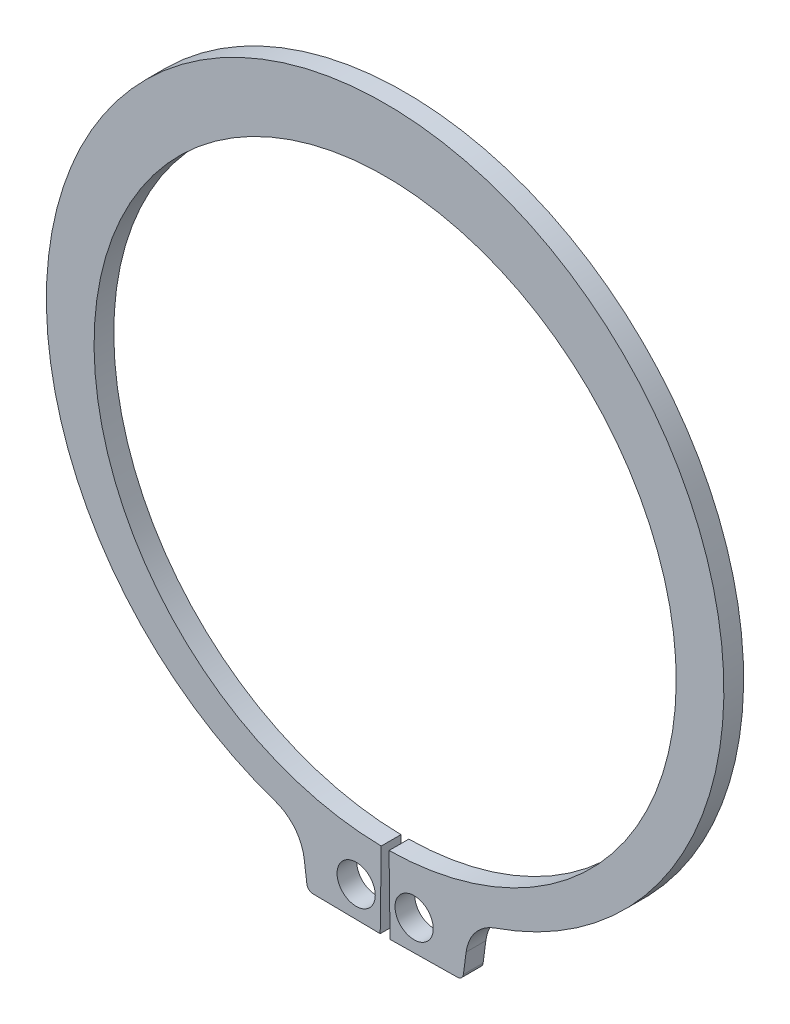
SolidWorks part; units mm, degrees
ref_plane "Plane1" through (0, 0, 0) normal (0, 0, 1) x (1, 0, 0)
ref_plane "Plane2" through (0, 0, 0) normal (0, 1, 0) x (1, 0, 0)
ref_plane "Plane3" through (0, 0, 0) normal (1, 0, 0) x (0, 0, -1)
sketch "Clipboard" plane through (0, 0, 0) normal (0, 0, 1) x (1, 0, 0)
  line L0 (0, 0) -> (5.1, 0)
  line L1 (0, 0) -> (0, 2.7)
  line L2 (0, 0) -> (0, -6.2)
  circle A0 centre (0, 0) radius 1.55
  circle A1 centre (0, 0) radius 25
  dimension "HoleDia" = 3.1
  dimension "ShaftDia" = 50
  dimension "LargeSection" = 5.1
  dimension "SmallSection" = 2.7
  dimension "LugSection" = 6.2
sketch "BodySke" plane through (0, 0, 0) normal (0, 0, 1) x (1, 0, 0)
  line L0 (-1.5431, 0) -> (1.5431, 0) construction
  line L1 (0, 0) -> (0, 28.7) construction
  line L2 (0.3168, -23.5979) -> (0.4, -29.7973)
  line L3 (-0.3168, -23.5979) -> (-0.4, -29.7973)
  line L4 (0, 0) -> (10.0358, -28.0593) construction
  line L5 (0, 0) -> (-10.0358, -28.0593) construction
  line L6 (0.4, -29.7973) -> (5.855, -29.7241)
  line L7 (6.5661, -27.6025) -> (6.344, -29.2894)
  line L8 (-6.5661, -27.6025) -> (-6.344, -29.2894)
  line L9 (-0.4, -29.7973) -> (-5.855, -29.7241)
  circle A0 centre (0, 0) radius 23.6 construction
  arc A1 (0.3168, -23.5979) -> (-0.3168, -23.5979) centre (0, 0) ccw
  arc A2 (8.8571, -24.7637) -> (-8.8571, -24.7637) centre (0, 1.2345) ccw construction
  arc A3 (0.4, -29.7973) -> (7.4625, -28.8505) centre (0, 0) ccw construction
  arc A4 (8.9016, -24.7485) -> (6.5661, -27.6025) centre (10.0358, -28.0593) ccw
  arc A5 (-6.5661, -27.6025) -> (-8.9016, -24.7485) centre (-10.0358, -28.0593) ccw
  arc A6 (-7.4625, -28.8505) -> (-0.4, -29.7973) centre (0, 0) ccw construction
  arc A7 (8.9016, -24.7485) -> (-8.9016, -24.7485) centre (0, 1.2345) ccw
  arc A8 (-6.7024, -26.5676) -> (6.7024, -26.5676) centre (0, 0) ccw construction
  circle A9 centre (2.35, -27.299) radius 1.55
  circle A10 centre (-2.35, -27.299) radius 1.55
  arc A11 (6.344, -29.2894) -> (5.855, -29.7241) centre (5.8483, -29.2241) cw
  arc A12 (-6.344, -29.2894) -> (-5.855, -29.7241) centre (-5.8483, -29.2241) ccw
  point P28 (6.3674, -29.1118)
  point P31 (-6.3674, -29.1118)
  dimension "GrooveDia" = 47.2
  dimension "LugRad" = 29.8
  dimension "HoleOffsetRad" = 27.4
  dimension "HoleDia" = 3.1
  dimension "D3" = 0.5
  dimension "LargeRad" = 28.7
  dimension "SmallRad" = 26.3
  dimension "SmallAngle" = 39.361
  dimension "D2" = 15
  dimension "HoleSpacing" = 4.7
  dimension "Gap" = 0.8
extrude "Body" add sketch "BodySke" against normal blind 1.6
sketch "NotSke" plane through (0, 0, 0) normal (0, 0, 1) x (1, 0, 0)
  line L0 (2.35, -25.749) -> (2.35, -28.849)
  line L1 (2.35, -28.849) -> (-2.35, -28.849)
  line L2 (-2.35, -28.849) -> (-2.35, -25.749)
  line L3 (-2.35, -25.749) -> (2.35, -25.749)
  circle A0 centre (2.35, -27.299) radius 1.55 construction
  circle A1 centre (-2.35, -27.299) radius 1.55 construction
extrude "Notch" [suppressed] cut sketch "NotSke" against normal through all
equation "' \"ShaftDia@Clipboard\" = 4"
equation "' \"Thickness@Body\" = 0.25"
equation "' \"GrooveDia@BodySke\" = 3.8"
equation "' \"LugSection@Clipboard\" = 1.35"
equation "' \"LargeSection@Clipboard\" = 0.65"
equation "' \"SmallSection@Clipboard\" = 0.4"
equation "' \"HoleDia@Clipboard\" = 0.6"
equation "' \"ShaftDia@Clipboard\" = 15"
equation "' \"Thickness@Body\" = 0.9"
equation "' \"GrooveDia@BodySke\" = 14.15"
equation "' \"LugSection@Clipboard\" = 2.8"
equation "' \"LargeSection@Clipboard\" = 1.8"
equation "' \"SmallSection@Clipboard\" = 1.05"
equation "' \"HoleDia@Clipboard\" = 1.2"
equation "\"Gap@BodySke\" =  \"Thickness@Body\" / 2"
equation "\"LargeRad@BodySke\" =  \"GrooveDia@BodySke\" / 2 +  \"LargeSection@Clipboard\""
equation "\"SmallRad@BodySke\" =  \"GrooveDia@BodySke\" / 2 +  \"SmallSection@Clipboard\""
equation "\"LugRad@BodySke\" = \"GrooveDia@BodySke\" / 2 + \"LugSection@Clipboard\""
equation "\"HoleOffsetRad@BodySke\" = (  \"ShaftDia@Clipboard\" / 2 + \"LugRad@BodySke\" ) / 2"
equation "\"HoleSpacing@BodySke\" = \"Gap@BodySke\"  * 2 +  \"HoleDia@Clipboard\""
equation "\"HoleDia@BodySke\" =  \"HoleDia@Clipboard\""
equation "\"SmallAngle@BodySke\" = atn(\"HoleSpacing@BodySke\" / 2 / sqr(\"HoleOffsetRad@BodySke\"  * \"HoleOffsetRad@BodySke\" - (\"HoleSpacing@BodySke\" / 2) * (\"HoleSpacing@BodySke\" / 2) ))  * 8 * ( 180 / 3.141593)"
